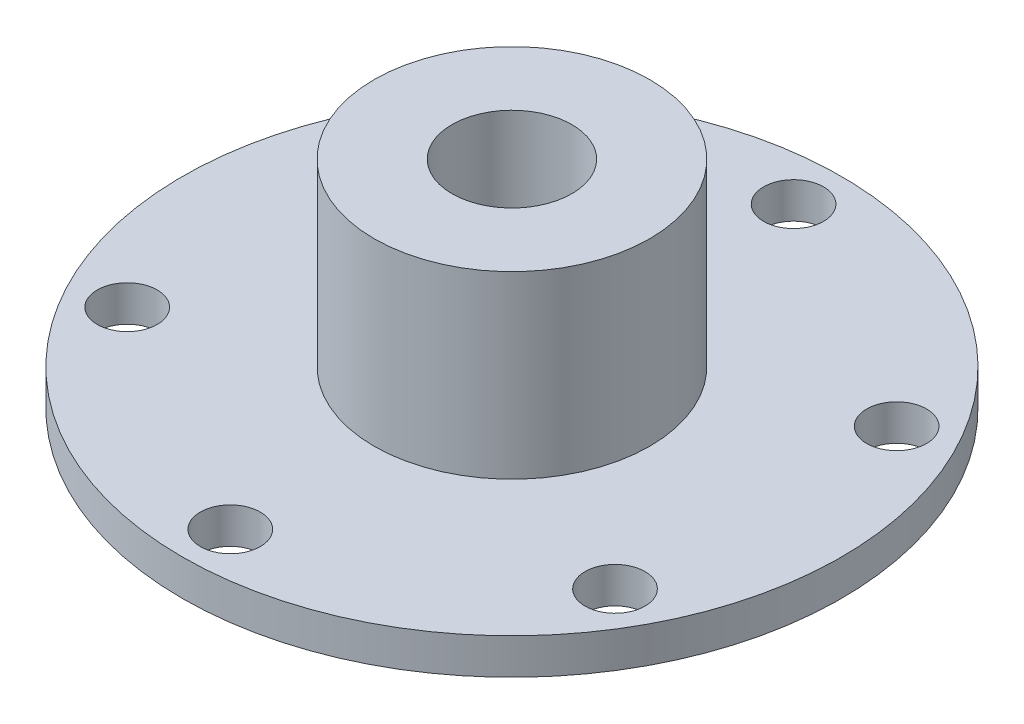
SolidWorks part; units mm, degrees
material "Alumina"
ref_plane "Front Plane" through (0, 0, 0) normal (0, 0, 1) x (1, 0, 0)
ref_plane "Top Plane" through (0, 0, 0) normal (0, 1, 0) x (1, 0, 0)
ref_plane "Right Plane" through (0, 0, 0) normal (1, 0, 0) x (0, 0, -1)
sketch "Sketch1" plane through (0, 0, 0) normal (0, 1, 0) x (1, 0, 0)
  circle A0 centre (0, 0) radius 27.5
  circle A1 centre (0, 0) radius 5
  circle A2 centre (0, 23.5) radius 2.5
  circle A3 centre (20.3516, 11.75) radius 2.5
  circle A4 centre (20.3516, -11.75) radius 2.5
  circle A5 centre (0, -23.5) radius 2.5
  circle A6 centre (-20.3516, -11.75) radius 2.5
  circle A7 centre (-20.3516, 11.75) radius 2.5
  point P6 (-20.5256, -9.8523)
  point P7 (0, 0)
  point P8 (0, 0)
  point P15 (0, 0)
  dimension "D1" = 55
  dimension "D2" = 10
  dimension "D3" = 5
  dimension "D4" = 23.5
  dimension "D5" = 6
extrude "Boss-Extrude1" add sketch "Sketch1" along normal blind 3
sketch "Sketch2" plane through (0, 3, 0) normal (0, 1, 0) x (1, 0, 0)
  circle A0 centre (0, 0) radius 11.5
  circle A1 centre (0, 0) radius 5 construction
  circle A2 centre (0, 0) radius 5
  dimension "D1" = 23
extrude "Boss-Extrude2" add sketch "Sketch2" along normal blind 15
